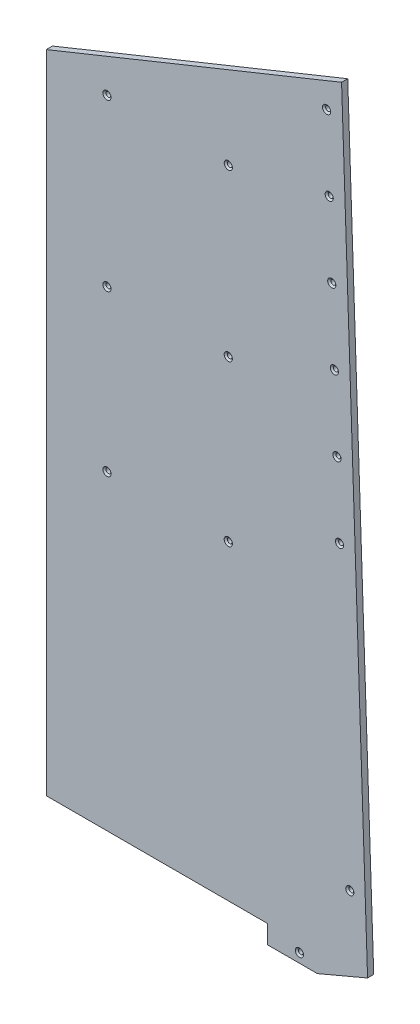
SolidWorks part; units mm, degrees
material "MDF"
ref_plane "Front" through (0, 0, 0) normal (0, 0, 1) x (1, 0, 0)
ref_plane "Top" through (0, 0, 0) normal (0, 1, 0) x (1, 0, 0)
ref_plane "Right" through (0, 0, 0) normal (1, 0, 0) x (0, 0, -1)
sketch "Sketch1" plane through (0, 0, 0) normal (0, 0, 1) x (1, 0, 0)
  line L0 (2683.51, 6621.1958) -> (2683.51, 5955.03)
  line L13 (2810.51, 5935.98) -> (2931.8099, 5935.98) construction
  line L15 (2683.51, 6621.1958) -> (2987.93, 6744.1895)
  line L16 (2683.51, 6621.1958) -> (3343.691, 6887.9262) construction
  line L17 (2999.2893, 6417.6477) -> (2992.9976, 6598.5133) construction
  line L18 (2987.93, 6744.1895) -> (3014.7288, 5957.9381)
  line L19 (3014.7288, 5957.9381) -> (2962.9987, 5935.98)
  line L20 (2977.1624, 5941.9922) -> (3014.7288, 5957.9381) construction
  line L21 (2962.9987, 5935.98) -> (2911.73, 5935.98)
  line L24 (2911.73, 5955.03) -> (2683.51, 5955.03)
  line L25 (2911.73, 5955.03) -> (2911.73, 5935.98)
  dimension "D1" = 76.2
extrude "Boss-Extrude1" add sketch "Sketch1" along normal blind 6.35 contours L15 L25 L21 L19 L18
sketch "Sketch2" plane through (0, 0, 6.35) normal (0, 0, 1) x (1, 0, 0)
  line L0 (2933.6977, 6602.1458) -> (2933.6977, 6621.1958) construction
  line L1 (2683.51, 6602.1458) -> (2933.6977, 6602.1458) construction
  line L2 (2933.6977, 6621.1958) -> (2683.51, 6621.1958) construction
  line L3 (2933.6977, 6621.1958) -> (2683.51, 6621.1958)
  line L4 (2933.6977, 6602.1458) -> (2933.6977, 6621.1958)
  line L5 (2683.51, 6602.1458) -> (2933.6977, 6602.1458)
  line L6 (2683.51, 6621.1958) -> (2683.51, 6602.1458)
extrude "Boss-Extrude2" add sketch "Sketch2" against normal up to surface (6.35 mm away)
hole_wizard "CSK for #8 Flat Head Machine Screw (100)2" positions "Sketch5" profile "Sketch6" countersink size "#8" standard "ANSI Inch"
sketch "Sketch5" plane through (0, 0, 6.35) normal (0, 0, 1) x (1, 0, 0)
  point P0 (2871.1508, 6611.6708)
  point P3 (2746.0569, 6611.6708)
  point P6 (2746.0569, 6440.805)
  point P9 (2871.1508, 6440.805)
  point P12 (2746.0569, 6275.705)
  point P15 (2871.1508, 6275.705)
  point P21 (2944.4462, 5945.505)
  point P24 (2996.4396, 6026.7952)
  point P27 (2985.8022, 6331.4095)
  point P30 (2983.1429, 6407.5631)
  point P33 (2980.4835, 6483.7167)
  point P36 (2977.8242, 6559.8703)
  point P39 (2975.1649, 6636.0239)
  point P42 (2972.5055, 6712.1774)
sketch "Sketch6" plane through (2871.1508, 6611.6708, 6.35) normal (1, 0, 0) x (0, -1, 0)
  line L0 (0, 0) -> (0, 6.35)
  line L1 (0, 6.35) -> (2.4574, 6.35)
  line L2 (2.4574, 6.35) -> (2.4574, 1.4759)
  line L3 (2.4574, 1.4759) -> (4.2164, 0)
  line L5 (4.2164, 0) -> (0, 0)
  line L6 (-2.4574, 1.4759) -> (-4.2164, 0) construction
  line L11 (0, -6.35) -> (0, 107.95) construction
  dimension "Thru Hole Dia." = 4.9149
  dimension "Thru Hole Depth" = 6.35
  dimension "Near C'Sink Dia." = 8.4328
  dimension "Near C'Sink Angle" = 100
